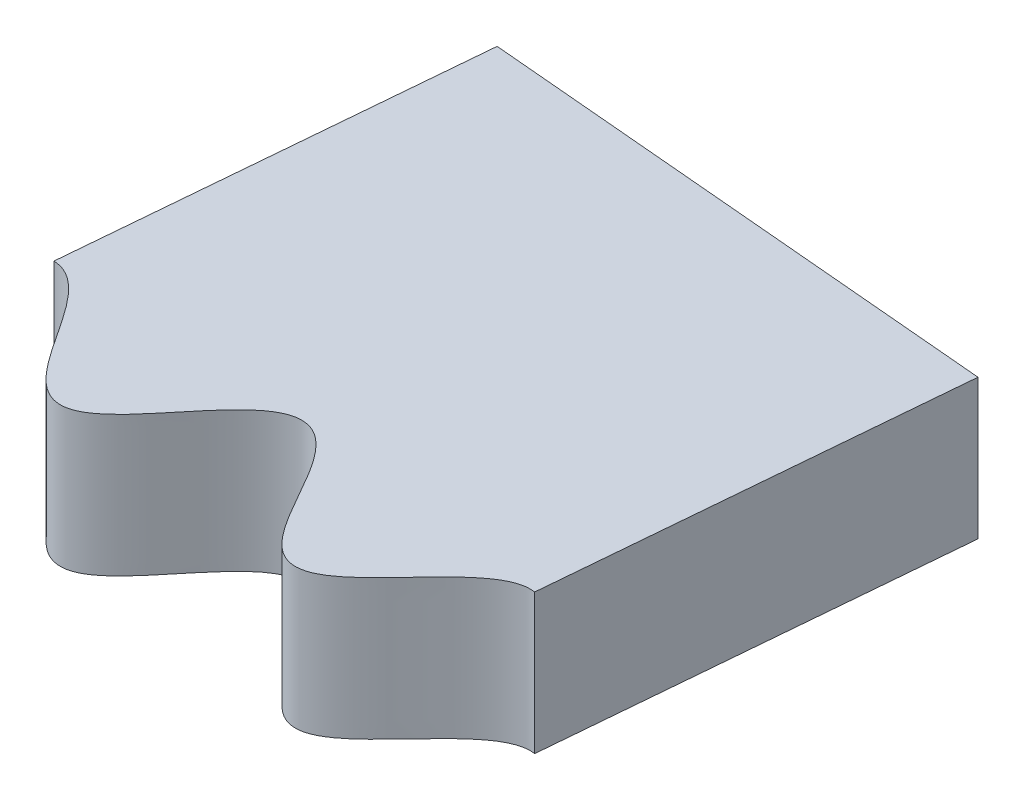
SolidWorks part; units mm, degrees
ref_plane "Front Plane" through (0, 0, 0) normal (0, 0, 1) x (1, 0, 0)
ref_plane "Top Plane" through (0, 0, 0) normal (0, 1, 0) x (1, 0, 0)
ref_plane "Right Plane" through (0, 0, 0) normal (1, 0, 0) x (0, 0, -1)
sketch "Sketch1" plane through (0, 0, 0) normal (0, 1, 0) x (1, 0, 0)
  line L0 (0, 80) -> (0, 90)
  line L1 (80, 0) -> (90, 0)
  arc A0 (0, 90) -> (90, 0) centre (0, 0) cw
  spline S0 degree 4 number of poles 687 (78.7091, -11.4049) -> (-11.4049, 78.7091) construction
  spline S1 degree 4 number of poles 577 (80, 0) -> (0, 80)
  dimension "D1" = 90
extrude "Boss-Extrude1" add sketch "Sketch1" along normal blind 3
sketch "Sketch3" plane through (0, 3, 0) normal (0, 1, 0) x (1, 0, 0)
  line L0 (1.418, 81.2373) -> (2.1823, 89.9735)
  line L3 (0, 90) -> (0, 80) construction
  line L4 (0, 90) -> (0, 80)
  arc A1 (90, 0) -> (0, 90) centre (0, 0) ccw construction
  arc A3 (2.1823, 89.9735) -> (0, 90) centre (0, 0) ccw
  spline S1 degree 4 number of poles 577 (0, 80) -> (26.9261, 74.8793) construction
  spline S2 degree 4 poles (0, 80) (0.0296, 80.0416) (0.0888, 80.1247) (0.255, 80.3557) (0.4282, 80.5807) (0.6286, 80.8143) (0.8513, 81.0183) (1.0518, 81.1561) (1.2271, 81.2234) (1.3512, 81.2381) (1.4148, 81.2374) (1.418, 81.2373) knots 0.077848 0.077848 0.077848 0.077848 0.077848 0.079019 0.080191 0.082534 0.083705 0.084877 0.086048 0.08722 0.087282 0.087282 0.087282 0.087282 0.087282
  dimension "D1" = 5
  dimension "D2" = 1
extrude "Cut-Extrude2" cut sketch "Sketch3" against normal through all both and the other way through all
sketch "Sketch2" plane through (0, 3, 0) normal (0, 1, 0) x (1, 0, 0)
  line L1 (12.7103, 80.2494) -> (13.4746, 88.9856)
  line L3 (1.418, 81.2373) -> (2.1823, 89.9735) construction
  arc A0 (90, 0) -> (2.1823, 89.9735) centre (0, 0) ccw construction
  arc A1 (90, 0) -> (13.4746, 88.9856) centre (0, 0) ccw
  spline S0 degree 4 number of poles 570 (1.3759, 81.2886) -> (80, 0) construction
  spline S2 degree 4 number of poles 517 (12.7103, 80.2494) -> (80, 0)
  dimension "D1" = 8
extrude "Cut-Extrude1" cut sketch "Sketch2" against normal through all both and the other way through all
sketch "Sketch4" plane through (0, 3, 0) normal (0, 1, 0) x (1, 0, 0)
  line L0 (2.1823, 89.9735) -> (13.4746, 88.9856)
  arc A0 (13.4746, 88.9856) -> (2.1823, 89.9735) centre (0, 0) ccw construction
  arc A1 (13.4746, 88.9856) -> (2.1823, 89.9735) centre (0, 0) ccw
extrude "Cut-Extrude3" cut sketch "Sketch4" against normal through all both and the other way through all
